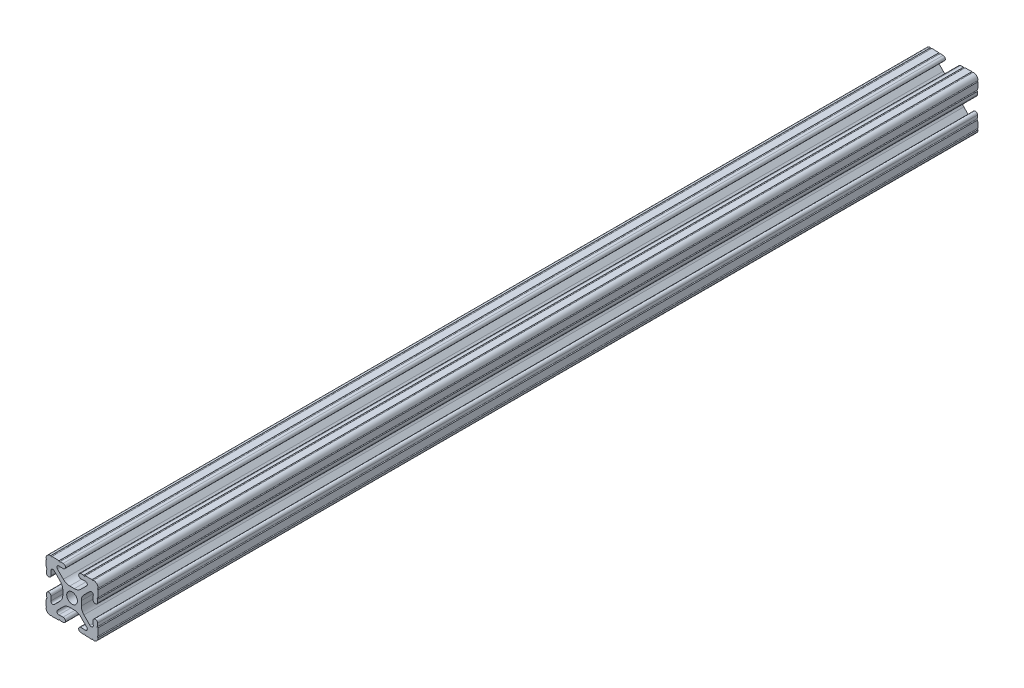
SolidWorks part; units mm, degrees
ref_plane "Front Plane" through (0, 0, 0) normal (0, 0, 1) x (1, 0, 0)
ref_plane "Top Plane" through (0, 0, 0) normal (0, 1, 0) x (1, 0, 0)
ref_plane "Right Plane" through (0, 0, 0) normal (1, 0, 0) x (0, 0, -1)
sketch "Sketch1" plane through (0, 0, 0) normal (0, 0, 1) x (1, 0, 0)
  line L0 (0, 12.7) -> (-12.7814, 12.7) construction
  line L1 (-4.5085, 0) -> (-4.5085, 2.9459)
  line L2 (-6.0437, 12.5461) -> (-10.0976, 12.6876) construction
  line L3 (-11.5616, 12.4229) -> (-4.3159, 12.1699) construction
  line L4 (-6.4364, 10.3486) -> (-6.3592, 12.5571) construction
  line L6 (-2.9459, 4.5085) -> (0, 4.5085)
  line L7 (0, 0) -> (0, 12.7) construction
  line L8 (0, 0) -> (-12.7814, 0) construction
  line L9 (0.7813, 0.7813) -> (-0.7813, -0.7813) construction
  line L10 (-2.9459, 4.5085) -> (-7.1484, 8.711)
  line L11 (-4.5085, 2.9459) -> (-8.711, 7.1484)
  line L13 (0, 0) -> (-12.7814, 12.7814) construction
  line L14 (-10.4131, 12.6987) -> (-4.3048, 12.4853)
  line L15 (-4.3048, 12.4853) -> (-4.382, 10.2769) construction
  line L16 (-4.382, 10.2769) -> (-6.4364, 10.3486)
  line L17 (-12.6987, 10.4131) -> (-12.4853, 4.3048)
  line L18 (-10.2769, 4.382) -> (-10.3486, 6.4364)
  circle A0 centre (0, 0) radius 2.6035
  arc A1 (-4.382, 10.2769) -> (-4.3048, 12.4853) centre (-4.3434, 11.3811) ccw
  arc A2 (-7.1484, 8.711) -> (-6.4364, 10.3486) centre (-6.4698, 9.3896) cw
  arc A3 (-8.711, 7.1484) -> (-10.3486, 6.4364) centre (-9.3896, 6.4698) ccw
  arc A4 (-10.2769, 4.382) -> (-12.4853, 4.3048) centre (-11.3811, 4.3434) cw
  arc A5 (-10.4131, 12.6987) -> (-12.6987, 10.4131) centre (-10.4902, 10.4902) ccw
  arc A6 (-10.4131, 12.6987) -> (-9.7821, 12.6766) centre (-10.0976, 12.6876) ccw
  arc A7 (-6.3592, 12.5571) -> (-5.7282, 12.5351) centre (-6.0437, 12.5461) ccw
  arc A8 (-12.5571, 6.3592) -> (-12.5351, 5.7282) centre (-12.5461, 6.0437) cw
  arc A9 (-12.6987, 10.4131) -> (-12.6766, 9.7821) centre (-12.6876, 10.0976) cw
  dimension "D1" = 5.207
  dimension "D5" = 14.859
  dimension "D9" = 2
  dimension "D2" = 25.4
  dimension "D12" = 0.6314
  dimension "D10" = 2.2098
  dimension "D3" = 9.017
  dimension "D4" = 9.017
  dimension "D6" = 25.4
  dimension "D7" = 6.477
  dimension "D8" = 2.2098
  dimension "D11" = 12.7
sketch "Sketch3" plane through (0, 0, 0) normal (0, 0, 1) x (1, 0, 0)
  line L0 (-2.9459, 4.5085) -> (0, 4.5085) construction
  line L1 (-2.9459, 4.5085) -> (-7.1484, 8.711) construction
  line L2 (-4.382, 10.2769) -> (-6.4364, 10.3486) construction
  line L3 (-10.4131, 12.6987) -> (-4.3048, 12.4853) construction
  line L4 (-4.5085, 0) -> (-4.5085, 2.9459) construction
  line L5 (-4.5085, 2.9459) -> (-8.711, 7.1484) construction
  line L6 (-10.2769, 4.382) -> (-10.3486, 6.4364) construction
  line L7 (-12.6987, 10.4131) -> (-12.4853, 4.3048) construction
  line L8 (-1.1153, 4.5085) -> (1.1153, 4.5085)
  line L9 (-4.2404, 5.803) -> (-7.1484, 8.711)
  line L10 (-4.382, 10.2769) -> (-6.4364, 10.3486)
  line L11 (-9.7821, 12.6766) -> (-6.3592, 12.5571)
  line L12 (-4.5085, -1.1153) -> (-4.5085, 1.1153)
  line L13 (-5.803, 4.2404) -> (-8.711, 7.1484)
  line L14 (-10.2769, 4.382) -> (-10.3486, 6.4364)
  line L15 (-12.6766, 9.7821) -> (-12.5571, 6.3592)
  line L16 (-5.7282, 12.5351) -> (-4.3048, 12.4853)
  line L17 (-12.5351, 5.7282) -> (-12.4853, 4.3048)
  line L18 (0, 0) -> (0, 12.7) construction
  line L19 (0, 0) -> (-12.7814, 0) construction
  line L20 (12.5351, 5.7282) -> (12.4853, 4.3048)
  line L21 (5.7282, 12.5351) -> (4.3048, 12.4853)
  line L22 (12.6766, 9.7821) -> (12.5571, 6.3592)
  line L23 (10.2769, 4.382) -> (10.3486, 6.4364)
  line L24 (5.803, 4.2404) -> (8.711, 7.1484)
  line L25 (4.5085, -1.1153) -> (4.5085, 1.1153)
  line L26 (9.7821, 12.6766) -> (6.3592, 12.5571)
  line L27 (4.382, 10.2769) -> (6.4364, 10.3486)
  line L28 (4.2404, 5.803) -> (7.1484, 8.711)
  line L29 (4.2404, -5.803) -> (7.1484, -8.711)
  line L30 (4.382, -10.2769) -> (6.4364, -10.3486)
  line L31 (9.7821, -12.6766) -> (6.3592, -12.5571)
  line L32 (5.803, -4.2404) -> (8.711, -7.1484)
  line L33 (10.2769, -4.382) -> (10.3486, -6.4364)
  line L34 (12.6766, -9.7821) -> (12.5571, -6.3592)
  line L35 (5.7282, -12.5351) -> (4.3048, -12.4853)
  line L36 (12.5351, -5.7282) -> (12.4853, -4.3048)
  line L37 (-12.5351, -5.7282) -> (-12.4853, -4.3048)
  line L38 (-5.7282, -12.5351) -> (-4.3048, -12.4853)
  line L39 (-12.6766, -9.7821) -> (-12.5571, -6.3592)
  line L40 (-10.2769, -4.382) -> (-10.3486, -6.4364)
  line L41 (-5.803, -4.2404) -> (-8.711, -7.1484)
  line L42 (-9.7821, -12.6766) -> (-6.3592, -12.5571)
  line L43 (-4.382, -10.2769) -> (-6.4364, -10.3486)
  line L44 (-4.2404, -5.803) -> (-7.1484, -8.711)
  line L45 (-1.1153, -4.5085) -> (1.1153, -4.5085)
  arc A0 (-10.4131, 12.6987) -> (-9.7821, 12.6766) centre (-10.0976, 12.6876) ccw construction
  arc A1 (-6.4364, 10.3486) -> (-7.1484, 8.711) centre (-6.4698, 9.3896) ccw construction
  arc A2 (-4.382, 10.2769) -> (-4.3048, 12.4853) centre (-4.3434, 11.3811) ccw construction
  arc A3 (-8.711, 7.1484) -> (-10.3486, 6.4364) centre (-9.3896, 6.4698) ccw construction
  arc A4 (-12.4853, 4.3048) -> (-10.2769, 4.382) centre (-11.3811, 4.3434) ccw construction
  arc A5 (-6.3592, 12.5571) -> (-5.7282, 12.5351) centre (-6.0437, 12.5461) ccw construction
  arc A6 (-10.4131, 12.6987) -> (-12.6987, 10.4131) centre (-10.4902, 10.4902) ccw construction
  arc A7 (-12.6766, 9.7821) -> (-12.6987, 10.4131) centre (-12.6876, 10.0976) ccw construction
  arc A8 (-12.5351, 5.7282) -> (-12.5571, 6.3592) centre (-12.5461, 6.0437) ccw construction
  arc A9 (-10.4131, 12.6987) -> (-9.7821, 12.6766) centre (-10.0976, 12.6876) ccw
  arc A10 (-6.4364, 10.3486) -> (-7.1484, 8.711) centre (-6.4698, 9.3896) ccw
  arc A11 (-4.382, 10.2769) -> (-4.3048, 12.4853) centre (-4.3434, 11.3811) ccw
  arc A12 (-8.711, 7.1484) -> (-10.3486, 6.4364) centre (-9.3896, 6.4698) ccw
  arc A13 (-12.4853, 4.3048) -> (-10.2769, 4.382) centre (-11.3811, 4.3434) ccw
  arc A14 (-6.3592, 12.5571) -> (-5.7282, 12.5351) centre (-6.0437, 12.5461) ccw
  arc A15 (-10.4131, 12.6987) -> (-12.6987, 10.4131) centre (-10.4902, 10.4902) ccw
  arc A16 (-12.6766, 9.7821) -> (-12.6987, 10.4131) centre (-12.6876, 10.0976) ccw
  arc A17 (-12.5351, 5.7282) -> (-12.5571, 6.3592) centre (-12.5461, 6.0437) ccw
  arc A18 (-1.1153, 4.5085) -> (-4.2404, 5.803) centre (-1.1153, 8.9281) cw
  arc A19 (4.5085, 1.1153) -> (5.803, 4.2404) centre (8.9281, 1.1153) cw
  arc A20 (1.1153, 4.5085) -> (4.2404, 5.803) centre (1.1153, 8.9281) ccw
  arc A21 (-4.5085, 1.1153) -> (-5.803, 4.2404) centre (-8.9281, 1.1153) ccw
  arc A22 (12.5351, 5.7282) -> (12.5571, 6.3592) centre (12.5461, 6.0437) cw
  arc A23 (12.6766, 9.7821) -> (12.6987, 10.4131) centre (12.6876, 10.0976) cw
  arc A24 (10.4131, 12.6987) -> (12.6987, 10.4131) centre (10.4902, 10.4902) cw
  arc A25 (6.3592, 12.5571) -> (5.7282, 12.5351) centre (6.0437, 12.5461) cw
  arc A26 (12.4853, 4.3048) -> (10.2769, 4.382) centre (11.3811, 4.3434) cw
  arc A27 (8.711, 7.1484) -> (10.3486, 6.4364) centre (9.3896, 6.4698) cw
  arc A28 (4.382, 10.2769) -> (4.3048, 12.4853) centre (4.3434, 11.3811) cw
  arc A29 (6.4364, 10.3486) -> (7.1484, 8.711) centre (6.4698, 9.3896) cw
  arc A30 (10.4131, 12.6987) -> (9.7821, 12.6766) centre (10.0976, 12.6876) cw
  arc A31 (10.4131, -12.6987) -> (9.7821, -12.6766) centre (10.0976, -12.6876) ccw
  arc A32 (6.4364, -10.3486) -> (7.1484, -8.711) centre (6.4698, -9.3896) ccw
  arc A33 (4.382, -10.2769) -> (4.3048, -12.4853) centre (4.3434, -11.3811) ccw
  arc A34 (8.711, -7.1484) -> (10.3486, -6.4364) centre (9.3896, -6.4698) ccw
  arc A35 (12.4853, -4.3048) -> (10.2769, -4.382) centre (11.3811, -4.3434) ccw
  arc A36 (6.3592, -12.5571) -> (5.7282, -12.5351) centre (6.0437, -12.5461) ccw
  arc A37 (10.4131, -12.6987) -> (12.6987, -10.4131) centre (10.4902, -10.4902) ccw
  arc A38 (12.6766, -9.7821) -> (12.6987, -10.4131) centre (12.6876, -10.0976) ccw
  arc A39 (12.5351, -5.7282) -> (12.5571, -6.3592) centre (12.5461, -6.0437) ccw
  arc A40 (-4.5085, -1.1153) -> (-5.803, -4.2404) centre (-8.9281, -1.1153) cw
  arc A41 (1.1153, -4.5085) -> (4.2404, -5.803) centre (1.1153, -8.9281) cw
  arc A42 (4.5085, -1.1153) -> (5.803, -4.2404) centre (8.9281, -1.1153) ccw
  arc A43 (-1.1153, -4.5085) -> (-4.2404, -5.803) centre (-1.1153, -8.9281) ccw
  arc A44 (-12.5351, -5.7282) -> (-12.5571, -6.3592) centre (-12.5461, -6.0437) cw
  arc A45 (-12.6766, -9.7821) -> (-12.6987, -10.4131) centre (-12.6876, -10.0976) cw
  arc A46 (-10.4131, -12.6987) -> (-12.6987, -10.4131) centre (-10.4902, -10.4902) cw
  arc A47 (-6.3592, -12.5571) -> (-5.7282, -12.5351) centre (-6.0437, -12.5461) cw
  arc A48 (-12.4853, -4.3048) -> (-10.2769, -4.382) centre (-11.3811, -4.3434) cw
  arc A49 (-8.711, -7.1484) -> (-10.3486, -6.4364) centre (-9.3896, -6.4698) cw
  arc A50 (-4.382, -10.2769) -> (-4.3048, -12.4853) centre (-4.3434, -11.3811) cw
  arc A51 (-6.4364, -10.3486) -> (-7.1484, -8.711) centre (-6.4698, -9.3896) cw
  arc A52 (-10.4131, -12.6987) -> (-9.7821, -12.6766) centre (-10.0976, -12.6876) cw
  circle A53 centre (0, 0) radius 2.6035 construction
  circle A54 centre (0, 0) radius 2.6035
  point P135 (4.5085, 0)
  dimension "D2" = 4.4196
extrude "Extrude1" add sketch "Sketch3" along normal mid plane 429.1
ref_plane "Plane1" through (12.4853, 4.3048, 214.55) normal (0.0349, 0.9994, 0) x (0.9994, -0.0349, 0)
sketch "Sketch5" plane through (4.5085, 0, 0) normal (1, 0, 0) x (0, 0, -1)
  line L1 (214.55, -1.1153) -> (214.55, 1.1153) construction
  circle A0 centre (199.55, 0) radius 6.35
  dimension "D1" = 12.7
  dimension "D2" = 15
equation "\"D10@Sketch1\" = \"D8@Sketch1\""
equation "\"D11@Sketch1\" = \"D6@Sketch1\"/2"
equation "\"D12@Sketch1\" = \"D8@Sketch1\"/3.5"
equation "\"D2@Sketch3\" = \"D8@Sketch1\"*2"
